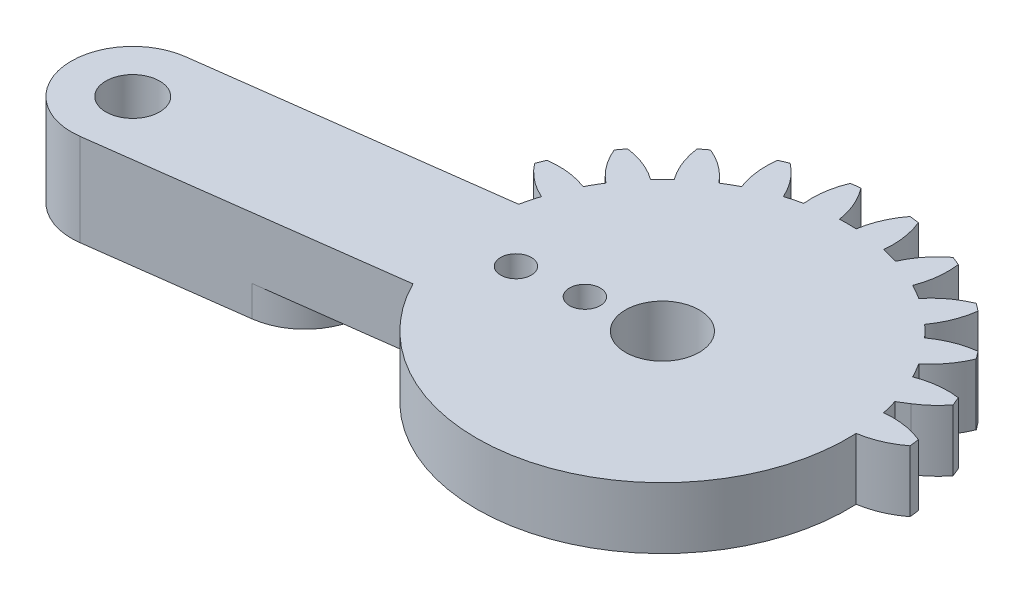
SolidWorks part; units mm, degrees
ref_plane "Front Plane" through (0, 0, 0) normal (0, 0, 1) x (1, 0, 0)
ref_plane "Top Plane" through (0, 0, 0) normal (0, 1, 0) x (1, 0, 0)
ref_plane "Right Plane" through (0, 0, 0) normal (1, 0, 0) x (0, 0, -1)
sketch "Sketch1" plane through (0, 0, 0) normal (0, 1, 0) x (1, 0, 0)
  line L0 (20.6437, 4) -> (2.0816, 4)
  line L1 (2.0816, -4) -> (20.6437, -4)
  arc A0 (2.0816, 4) -> (3.5217, 5.3071) centre (-0.7683, 8.5867) ccw
  arc A1 (3.5217, 5.3071) -> (3.2829, 5.8838) centre (-10.1063, 0) ccw
  arc A2 (3.2829, 5.8838) -> (0.6271, 5.5703) centre (2.5684, 0.5313) ccw
  arc A3 (0.6271, 5.5703) -> (0.0844, 6.5103) centre (-10.1063, 0) ccw
  arc A4 (0.0844, 6.5103) -> (1.6838, 8.6535) centre (-3.3089, 10.711) ccw
  arc A5 (1.6838, 8.6535) -> (1.3038, 9.1487) centre (-10.1063, 0) ccw
  arc A6 (1.3038, 9.1487) -> (-1.1803, 8.1585) centre (1.999, 3.7936) ccw
  arc A7 (-1.1803, 8.1585) -> (-1.9479, 8.926) centre (-10.1063, 0) ccw
  arc A8 (-1.9479, 8.926) -> (-0.9576, 11.4102) centre (-6.3127, 12.1053) ccw
  arc A9 (-0.9576, 11.4102) -> (-1.4528, 11.7901) centre (-10.1063, 0) ccw
  arc A10 (-1.4528, 11.7901) -> (-3.596, 10.1907) centre (0.6046, 6.7975) ccw
  arc A11 (-3.596, 10.1907) -> (-4.5361, 10.7334) centre (-10.1063, 0) ccw
  arc A12 (-4.5361, 10.7334) -> (-4.2225, 13.3892) centre (-9.5751, 12.6747) ccw
  arc A13 (-4.2225, 13.3892) -> (-4.7992, 13.6281) centre (-10.1063, 0) ccw
  arc A14 (-4.7992, 13.6281) -> (-6.4554, 11.5285) centre (-1.5196, 9.3381) ccw
  arc A15 (-6.4554, 11.5285) -> (-7.5039, 11.8094) centre (-10.1063, 0) ccw
  arc A16 (-7.5039, 11.8094) -> (-7.8884, 14.4558) centre (-12.8736, 12.3803) ccw
  arc A17 (-7.8884, 14.4558) -> (-8.5072, 14.5373) centre (-10.1063, 0) ccw
  arc A18 (-8.5072, 14.5373) -> (-9.5636, 12.0806) centre (-4.2291, 11.2423) ccw
  arc A19 (-9.5636, 12.0806) -> (-10.6491, 12.0806) centre (-10.1063, 0) ccw
  arc A20 (-10.6491, 12.0806) -> (-11.7054, 14.5373) centre (-15.9836, 11.2423) ccw
  arc A21 (-11.7054, 14.5373) -> (-12.3243, 14.4558) centre (-10.1063, 0) ccw
  arc A22 (-12.3243, 14.4558) -> (-12.7088, 11.8094) centre (-7.3391, 12.3803) ccw
  arc A23 (-12.7088, 11.8094) -> (-13.7573, 11.5285) centre (-10.1063, 0) ccw
  arc A24 (-13.7573, 11.5285) -> (-15.4135, 13.6281) centre (-18.6931, 9.3381) ccw
  arc A25 (-15.4135, 13.6281) -> (-15.9901, 13.3892) centre (-10.1063, 0) ccw
  arc A26 (-15.9901, 13.3892) -> (-15.6766, 10.7334) centre (-10.6376, 12.6747) ccw
  arc A27 (-15.6766, 10.7334) -> (-16.6166, 10.1907) centre (-10.1063, 0) ccw
  arc A28 (-16.6166, 10.1907) -> (-18.7599, 11.7901) centre (-20.8173, 6.7975) ccw
  arc A29 (-18.7599, 11.7901) -> (-19.255, 11.4102) centre (-10.1063, 0) ccw
  arc A30 (-19.255, 11.4102) -> (-18.2648, 8.926) centre (-13.9, 12.1053) ccw
  arc A31 (-18.2648, 8.926) -> (-19.0324, 8.1585) centre (-10.1063, 0) ccw
  arc A32 (-19.0324, 8.1585) -> (-21.5165, 9.1487) centre (-22.2117, 3.7936) ccw
  arc A33 (-21.5165, 9.1487) -> (-21.8965, 8.6535) centre (-10.1063, 0) ccw
  arc A34 (-21.8965, 8.6535) -> (-20.2971, 6.5103) centre (-16.9038, 10.711) ccw
  arc A35 (-20.2971, 6.5103) -> (-20.8398, 5.5703) centre (-10.1063, 0) ccw
  arc A36 (-20.8398, 5.5703) -> (-23.4956, 5.8838) centre (-22.7811, 0.5313) ccw
  arc A37 (-23.4956, 5.8838) -> (-23.7344, 5.3071) centre (-10.1063, 0) ccw
  arc A38 (-23.7344, 5.3071) -> (-21.6348, 3.6509) centre (-19.4444, 8.5867) ccw
  arc A39 (-21.6348, 3.6509) -> (-21.9157, 2.6025) centre (-10.1063, 0) ccw
  arc A40 (-21.9157, 2.6025) -> (-24.5622, 2.2179) centre (-22.4867, -2.7673) ccw
  arc A41 (-24.5622, 2.2179) -> (-24.6437, 1.5991) centre (-10.1063, 0) ccw
  arc A42 (-24.6437, 1.5991) -> (-22.1869, 0.5427) centre (-21.3486, 5.8773) ccw
  arc A43 (-22.1869, 0.5427) -> (-22.1869, -0.5427) centre (-10.1063, 0) ccw
  arc A44 (-22.1869, -0.5427) -> (-24.6437, -1.5991) centre (-21.3486, -5.8773) ccw
  arc A45 (-24.6437, -1.5991) -> (-24.5622, -2.2179) centre (-10.1063, 0) ccw
  arc A46 (-24.5622, -2.2179) -> (-21.9157, -2.6025) centre (-22.4867, 2.7673) ccw
  arc A47 (-21.9157, -2.6025) -> (-21.6348, -3.6509) centre (-10.1063, 0) ccw
  arc A48 (-21.6348, -3.6509) -> (-23.7344, -5.3071) centre (-19.4444, -8.5867) ccw
  arc A49 (-23.7344, -5.3071) -> (-23.4956, -5.8838) centre (-10.1063, 0) ccw
  arc A50 (-23.4956, -5.8838) -> (-20.8398, -5.5703) centre (-22.7811, -0.5313) ccw
  arc A51 (-20.8398, -5.5703) -> (-20.2971, -6.5103) centre (-10.1063, 0) ccw
  arc A52 (-20.2971, -6.5103) -> (-21.8965, -8.6535) centre (-16.9038, -10.711) ccw
  arc A53 (-21.8965, -8.6535) -> (-21.5165, -9.1487) centre (-10.1063, 0) ccw
  arc A54 (-21.5165, -9.1487) -> (-19.0324, -8.1585) centre (-22.2117, -3.7936) ccw
  arc A55 (-19.0324, -8.1585) -> (-18.2648, -8.926) centre (-10.1063, 0) ccw
  arc A56 (-18.2648, -8.926) -> (-19.255, -11.4102) centre (-13.9, -12.1053) ccw
  arc A57 (-19.255, -11.4102) -> (-18.7599, -11.7901) centre (-10.1063, 0) ccw
  arc A58 (-18.7599, -11.7901) -> (-16.6166, -10.1907) centre (-20.8173, -6.7975) ccw
  arc A59 (-16.6166, -10.1907) -> (-15.6766, -10.7334) centre (-10.1063, 0) ccw
  arc A60 (-15.6766, -10.7334) -> (-15.9901, -13.3892) centre (-10.6376, -12.6747) ccw
  arc A61 (-15.9901, -13.3892) -> (-15.4135, -13.6281) centre (-10.1063, 0) ccw
  arc A62 (-15.4135, -13.6281) -> (-13.7573, -11.5285) centre (-18.6931, -9.3381) ccw
  arc A63 (-13.7573, -11.5285) -> (-12.7088, -11.8094) centre (-10.1063, 0) ccw
  arc A64 (-12.7088, -11.8094) -> (-12.3243, -14.4558) centre (-7.3391, -12.3803) ccw
  arc A65 (-12.3243, -14.4558) -> (-11.7054, -14.5373) centre (-10.1063, 0) ccw
  arc A66 (-11.7054, -14.5373) -> (-10.6491, -12.0806) centre (-15.9836, -11.2423) ccw
  arc A67 (-10.6491, -12.0806) -> (-9.5636, -12.0806) centre (-10.1063, 0) ccw
  arc A68 (-9.5636, -12.0806) -> (-8.5072, -14.5373) centre (-4.2291, -11.2423) ccw
  arc A69 (-8.5072, -14.5373) -> (-7.8884, -14.4558) centre (-10.1063, 0) ccw
  arc A70 (-7.8884, -14.4558) -> (-7.5039, -11.8094) centre (-12.8736, -12.3803) ccw
  arc A71 (-7.5039, -11.8094) -> (-6.4554, -11.5285) centre (-10.1063, 0) ccw
  arc A72 (-6.4554, -11.5285) -> (-4.7992, -13.6281) centre (-1.5196, -9.3381) ccw
  arc A73 (-4.7992, -13.6281) -> (-4.2225, -13.3892) centre (-10.1063, 0) ccw
  arc A74 (-4.2225, -13.3892) -> (-4.5361, -10.7334) centre (-9.5751, -12.6747) ccw
  arc A75 (-4.5361, -10.7334) -> (-3.596, -10.1907) centre (-10.1063, 0) ccw
  arc A76 (-3.596, -10.1907) -> (-1.4528, -11.7901) centre (0.6046, -6.7975) ccw
  arc A77 (-1.4528, -11.7901) -> (-0.9576, -11.4102) centre (-10.1063, 0) ccw
  arc A78 (-0.9576, -11.4102) -> (-1.9479, -8.926) centre (-6.3127, -12.1053) ccw
  arc A79 (-1.9479, -8.926) -> (-1.1803, -8.1585) centre (-10.1063, 0) ccw
  arc A80 (-1.1803, -8.1585) -> (1.3038, -9.1487) centre (1.999, -3.7936) ccw
  arc A81 (1.3038, -9.1487) -> (1.6838, -8.6535) centre (-10.1063, 0) ccw
  arc A82 (1.6838, -8.6535) -> (0.0844, -6.5103) centre (-3.3089, -10.711) ccw
  arc A83 (0.0844, -6.5103) -> (0.6271, -5.5703) centre (-10.1063, 0) ccw
  arc A84 (0.6271, -5.5703) -> (3.2829, -5.8838) centre (2.5684, -0.5313) ccw
  arc A85 (3.2829, -5.8838) -> (3.5217, -5.3071) centre (-10.1063, 0) ccw
  arc A86 (3.5217, -5.3071) -> (2.0816, -4) centre (-0.7683, -8.5867) ccw
  arc A87 (20.6437, -4) -> (20.6437, 4) centre (20.6437, 0) ccw
  circle A88 centre (-10.1063, 0) radius 1.5
  circle A89 centre (20.6437, 0) radius 1.5
  dimension "D1" = 3
  dimension "D2" = 3
extrude "Boss-Extrude1" add sketch "Sketch1" along normal blind 4
sketch "Sketch3" plane through (0, 4, 0) normal (0, 1, 0) x (1, 0, 0)
  line L0 (-10.1063, 0) -> (-40.8563, 0) construction
  line L1 (-10.1063, 0) -> (-40.5933, -4.0137)
  line L2 (-10.6284, 3.9658) -> (-41.1154, -0.0479)
  line L3 (-9.5842, -3.9658) -> (-40.0712, -7.9795)
  line L4 (-10.1063, 0) -> (-4.5096, 13.5117) construction
  line L5 (-10.1063, 0) -> (-8.1974, 14.4999) construction
  circle A0 centre (-10.1063, 0) radius 1.5
  circle A1 centre (20.6437, 0) radius 1.5 construction
  circle A2 centre (20.6437, 0) radius 1.5
  circle A3 centre (-40.5933, -4.0137) radius 1.75
  circle A4 centre (-40.5933, -4.0137) radius 4
  circle A5 centre (-10.1063, 0) radius 4
  arc A6 (-4.2225, 13.3892) -> (-4.7992, 13.6281) centre (-10.1063, 0) ccw construction
  arc A7 (-7.8884, 14.4558) -> (-8.5072, 14.5373) centre (-10.1063, 0) ccw construction
  dimension "D2" = 3
  dimension "D5" = 3.5
  dimension "D6" = 8
  dimension "D7" = 8
  dimension "D1" = 30.75
  dimension "D4" = 7.5
extrude "Boss-Extrude2" add sketch "Sketch3" against normal blind 4
sketch "Sketch4" plane through (0, 4, 0) normal (0, 1, 0) x (1, 0, 0)
  line L0 (20.6437, 4) -> (2.0816, 4) construction
  line L1 (2.0816, -4) -> (20.6437, -4) construction
  line L2 (20.6437, 4) -> (2.0816, 4)
  line L3 (2.0816, -4) -> (20.6437, -4)
  line L4 (2.0816, 4) -> (1.4381, 3.6001)
  line L5 (-21.6245, -5.5509) -> (-20.8986, -5.4553)
  line L6 (-10.1063, 0) -> (0.0844, 6.5103) construction
  line L7 (-10.1063, 0) -> (1.9742, 0.5427) construction
  line L8 (-24.5755, 2.1296) -> (-41.1154, -0.0479)
  line L9 (-40.0712, -7.9795) -> (-23.5312, -5.8019)
  line L10 (2.0816, -4) -> (20.6437, -4)
  line L11 (20.6437, 4) -> (2.0816, 4)
  line L12 (-21.9429, 2.4762) -> (-41.1154, -0.0479)
  line L13 (-40.0712, -7.9795) -> (-21.6245, -5.5509)
  line L14 (2.0816, -4) -> (20.6437, -4)
  line L15 (20.6437, 4) -> (2.0816, 4)
  circle A0 centre (-10.1063, 0) radius 12.0927
  arc A1 (3.2829, 5.8838) -> (0.6271, 5.5703) centre (2.5684, 0.5313) ccw construction
  arc A2 (3.5217, 5.3071) -> (3.2829, 5.8838) centre (-10.1063, 0) ccw construction
  arc A3 (2.0816, 4) -> (3.5217, 5.3071) centre (-0.7683, 8.5867) ccw construction
  arc A4 (20.6437, -4) -> (20.6437, 4) centre (20.6437, 0) ccw construction
  arc A5 (3.5217, -5.3071) -> (2.0816, -4) centre (-0.7683, -8.5867) ccw construction
  arc A6 (3.2829, -5.8838) -> (3.5217, -5.3071) centre (-10.1063, 0) ccw construction
  arc A7 (0.6271, -5.5703) -> (3.2829, -5.8838) centre (2.5684, -0.5313) ccw construction
  arc A8 (3.2829, 5.8838) -> (0.6271, 5.5703) centre (2.5684, 0.5313) ccw
  arc A9 (3.5217, 5.3071) -> (3.2829, 5.8838) centre (-10.1063, 0) ccw
  arc A10 (2.0816, 4) -> (3.5217, 5.3071) centre (-0.7683, 8.5867) ccw
  arc A11 (20.6437, -4) -> (20.6437, 4) centre (20.6437, 0) ccw
  arc A12 (3.5217, -5.3071) -> (2.0816, -4) centre (-0.7683, -8.5867) ccw
  arc A13 (3.2829, -5.8838) -> (3.5217, -5.3071) centre (-10.1063, 0) ccw
  arc A14 (0.6271, -5.5703) -> (3.2829, -5.8838) centre (2.5684, -0.5313) ccw
  arc A15 (1.9742, 0.5427) -> (4.431, 1.5991) centre (1.1359, 5.8773) ccw
  arc A16 (4.3495, 2.2179) -> (1.7031, 2.6025) centre (2.274, -2.7673) ccw
  arc A17 (4.431, 1.5991) -> (4.3495, 2.2179) centre (-10.1063, 0) ccw
  arc A95 (-21.6348, 3.6509) -> (-21.9157, 2.6025) centre (-10.1063, 0) ccw
  arc A96 (-41.1154, -0.0479) -> (-40.0712, -7.9795) centre (-40.5933, -4.0137) ccw
  arc A97 (-20.2971, -6.5103) -> (-21.8965, -8.6535) centre (-16.9038, -10.711) ccw
  arc A98 (-21.8965, -8.6535) -> (-21.5165, -9.1487) centre (-10.1063, 0) ccw
  arc A99 (-21.5165, -9.1487) -> (-19.0324, -8.1585) centre (-22.2117, -3.7936) ccw
  arc A100 (-19.0324, -8.1585) -> (-18.2648, -8.926) centre (-10.1063, 0) ccw
  arc A101 (-18.2648, -8.926) -> (-19.255, -11.4102) centre (-13.9, -12.1053) ccw
  arc A102 (-19.255, -11.4102) -> (-18.7599, -11.7901) centre (-10.1063, 0) ccw
  arc A103 (-18.7599, -11.7901) -> (-16.6166, -10.1907) centre (-20.8173, -6.7975) ccw
  arc A104 (-16.6166, -10.1907) -> (-15.6766, -10.7334) centre (-10.1063, 0) ccw
  arc A105 (-15.6766, -10.7334) -> (-15.9901, -13.3892) centre (-10.6376, -12.6747) ccw
  arc A106 (-15.9901, -13.3892) -> (-15.4135, -13.6281) centre (-10.1063, 0) ccw
  arc A107 (-15.4135, -13.6281) -> (-13.7573, -11.5285) centre (-18.6931, -9.3381) ccw
  arc A108 (-13.7573, -11.5285) -> (-12.7088, -11.8094) centre (-10.1063, 0) ccw
  arc A109 (-12.7088, -11.8094) -> (-12.3243, -14.4558) centre (-7.3391, -12.3803) ccw
  arc A110 (-12.3243, -14.4558) -> (-11.7054, -14.5373) centre (-10.1063, 0) ccw
  arc A111 (-11.7054, -14.5373) -> (-10.6491, -12.0806) centre (-15.9836, -11.2423) ccw
  arc A112 (-10.6491, -12.0806) -> (-9.5636, -12.0806) centre (-10.1063, 0) ccw
  arc A113 (-9.5636, -12.0806) -> (-8.5072, -14.5373) centre (-4.2291, -11.2423) ccw
  arc A114 (-8.5072, -14.5373) -> (-7.8884, -14.4558) centre (-10.1063, 0) ccw
  arc A115 (-7.8884, -14.4558) -> (-7.5039, -11.8094) centre (-12.8736, -12.3803) ccw
  arc A116 (-7.5039, -11.8094) -> (-6.4554, -11.5285) centre (-10.1063, 0) ccw
  arc A117 (-6.4554, -11.5285) -> (-4.7992, -13.6281) centre (-1.5196, -9.3381) ccw
  arc A118 (-4.7992, -13.6281) -> (-4.2225, -13.3892) centre (-10.1063, 0) ccw
  arc A119 (-4.2225, -13.3892) -> (-4.5361, -10.7334) centre (-9.5751, -12.6747) ccw
  arc A120 (-4.5361, -10.7334) -> (-3.596, -10.1907) centre (-10.1063, 0) ccw
  arc A121 (-3.596, -10.1907) -> (-1.4528, -11.7901) centre (0.6046, -6.7975) ccw
  arc A122 (-1.4528, -11.7901) -> (-0.9576, -11.4102) centre (-10.1063, 0) ccw
  arc A123 (-0.9576, -11.4102) -> (-1.9479, -8.926) centre (-6.3127, -12.1053) ccw
  arc A124 (-1.9479, -8.926) -> (-1.1803, -8.1585) centre (-10.1063, 0) ccw
  arc A125 (-1.1803, -8.1585) -> (1.3038, -9.1487) centre (1.999, -3.7936) ccw
  arc A126 (1.3038, -9.1487) -> (1.6838, -8.6535) centre (-10.1063, 0) ccw
  arc A127 (1.6838, -8.6535) -> (0.0844, -6.5103) centre (-3.3089, -10.711) ccw
  arc A128 (0.0844, -6.5103) -> (0.6271, -5.5703) centre (-10.1063, 0) ccw
  arc A129 (0.6271, -5.5703) -> (3.2829, -5.8838) centre (2.5684, -0.5313) ccw
  arc A130 (3.2829, -5.8838) -> (3.5217, -5.3071) centre (-10.1063, 0) ccw
  arc A131 (3.5217, -5.3071) -> (2.0816, -4) centre (-0.7683, -8.5867) ccw
  arc A132 (20.6437, -4) -> (20.6437, 4) centre (20.6437, 0) ccw
  arc A133 (2.0816, 4) -> (3.5217, 5.3071) centre (-0.7683, 8.5867) ccw
  arc A134 (3.5217, 5.3071) -> (3.2829, 5.8838) centre (-10.1063, 0) ccw
  arc A135 (3.2829, 5.8838) -> (0.6271, 5.5703) centre (2.5684, 0.5313) ccw
  arc A136 (0.6271, 5.5703) -> (0.0844, 6.5103) centre (-10.1063, 0) ccw
  arc A137 (0.0844, 6.5103) -> (1.6838, 8.6535) centre (-3.3089, 10.711) ccw
  arc A138 (1.6838, 8.6535) -> (1.3038, 9.1487) centre (-10.1063, 0) ccw
  arc A139 (1.3038, 9.1487) -> (-1.1803, 8.1585) centre (1.999, 3.7936) ccw
  arc A140 (-1.1803, 8.1585) -> (-1.9479, 8.926) centre (-10.1063, 0) ccw
  arc A141 (-1.9479, 8.926) -> (-0.9576, 11.4102) centre (-6.3127, 12.1053) ccw
  arc A142 (-0.9576, 11.4102) -> (-1.4528, 11.7901) centre (-10.1063, 0) ccw
  arc A143 (-1.4528, 11.7901) -> (-3.596, 10.1907) centre (0.6046, 6.7975) ccw
  arc A144 (-3.596, 10.1907) -> (-4.5361, 10.7334) centre (-10.1063, 0) ccw
  arc A145 (-4.5361, 10.7334) -> (-4.2225, 13.3892) centre (-9.5751, 12.6747) ccw
  arc A146 (-4.2225, 13.3892) -> (-4.7992, 13.6281) centre (-10.1063, 0) ccw
  arc A147 (-4.7992, 13.6281) -> (-6.4554, 11.5285) centre (-1.5196, 9.3381) ccw
  arc A148 (-6.4554, 11.5285) -> (-7.5039, 11.8094) centre (-10.1063, 0) ccw
  arc A149 (-7.5039, 11.8094) -> (-7.8884, 14.4558) centre (-12.8736, 12.3803) ccw
  arc A150 (-7.8884, 14.4558) -> (-8.5072, 14.5373) centre (-10.1063, 0) ccw
  arc A151 (-8.5072, 14.5373) -> (-9.5636, 12.0806) centre (-4.2291, 11.2423) ccw
  arc A152 (-9.5636, 12.0806) -> (-10.6491, 12.0806) centre (-10.1063, 0) ccw
  arc A153 (-10.6491, 12.0806) -> (-11.7054, 14.5373) centre (-15.9836, 11.2423) ccw
  arc A154 (-11.7054, 14.5373) -> (-12.3243, 14.4558) centre (-10.1063, 0) ccw
  arc A155 (-12.3243, 14.4558) -> (-12.7088, 11.8094) centre (-7.3391, 12.3803) ccw
  arc A156 (-12.7088, 11.8094) -> (-13.7573, 11.5285) centre (-10.1063, 0) ccw
  arc A157 (-13.7573, 11.5285) -> (-15.4135, 13.6281) centre (-18.6931, 9.3381) ccw
  arc A158 (-15.4135, 13.6281) -> (-15.9901, 13.3892) centre (-10.1063, 0) ccw
  arc A159 (-15.9901, 13.3892) -> (-15.6766, 10.7334) centre (-10.6376, 12.6747) ccw
  arc A160 (-15.6766, 10.7334) -> (-16.6166, 10.1907) centre (-10.1063, 0) ccw
  arc A161 (-16.6166, 10.1907) -> (-18.7599, 11.7901) centre (-20.8173, 6.7975) ccw
  arc A162 (-18.7599, 11.7901) -> (-19.255, 11.4102) centre (-10.1063, 0) ccw
  arc A163 (-19.255, 11.4102) -> (-18.2648, 8.926) centre (-13.9, 12.1053) ccw
  arc A164 (-18.2648, 8.926) -> (-19.0324, 8.1585) centre (-10.1063, 0) ccw
  arc A165 (-19.0324, 8.1585) -> (-21.5165, 9.1487) centre (-22.2117, 3.7936) ccw
  arc A166 (-21.5165, 9.1487) -> (-21.8965, 8.6535) centre (-10.1063, 0) ccw
  arc A167 (-21.8965, 8.6535) -> (-20.2971, 6.5103) centre (-16.9038, 10.711) ccw
  arc A168 (-20.2971, 6.5103) -> (-20.8398, 5.5703) centre (-10.1063, 0) ccw
  arc A169 (-20.8398, 5.5703) -> (-23.4956, 5.8838) centre (-22.7811, 0.5313) ccw
  arc A170 (-23.4956, 5.8838) -> (-23.7344, 5.3071) centre (-10.1063, 0) ccw
  arc A171 (-23.7344, 5.3071) -> (-21.6348, 3.6509) centre (-19.4444, 8.5867) ccw
  arc A172 (-21.6348, 3.6509) -> (-21.9157, 2.6025) centre (-10.1063, 0) ccw
  arc A175 (-23.4956, -5.8838) -> (-20.8398, -5.5703) centre (-22.7811, -0.5313) ccw
  arc A176 (-41.1154, -0.0479) -> (-40.0712, -7.9795) centre (-40.5933, -4.0137) ccw
  arc A177 (-20.2971, -6.5103) -> (-21.8965, -8.6535) centre (-16.9038, -10.711) ccw
  arc A178 (-21.8965, -8.6535) -> (-21.5165, -9.1487) centre (-10.1063, 0) ccw
  arc A179 (-21.5165, -9.1487) -> (-19.0324, -8.1585) centre (-22.2117, -3.7936) ccw
  arc A180 (-19.0324, -8.1585) -> (-18.2648, -8.926) centre (-10.1063, 0) ccw
  arc A181 (-18.2648, -8.926) -> (-19.255, -11.4102) centre (-13.9, -12.1053) ccw
  arc A182 (-19.255, -11.4102) -> (-18.7599, -11.7901) centre (-10.1063, 0) ccw
  arc A183 (-18.7599, -11.7901) -> (-16.6166, -10.1907) centre (-20.8173, -6.7975) ccw
  arc A184 (-16.6166, -10.1907) -> (-15.6766, -10.7334) centre (-10.1063, 0) ccw
  arc A185 (-15.6766, -10.7334) -> (-15.9901, -13.3892) centre (-10.6376, -12.6747) ccw
  arc A186 (-15.9901, -13.3892) -> (-15.4135, -13.6281) centre (-10.1063, 0) ccw
  arc A187 (-15.4135, -13.6281) -> (-13.7573, -11.5285) centre (-18.6931, -9.3381) ccw
  arc A188 (-13.7573, -11.5285) -> (-12.7088, -11.8094) centre (-10.1063, 0) ccw
  arc A189 (-12.7088, -11.8094) -> (-12.3243, -14.4558) centre (-7.3391, -12.3803) ccw
  arc A190 (-12.3243, -14.4558) -> (-11.7054, -14.5373) centre (-10.1063, 0) ccw
  arc A191 (-11.7054, -14.5373) -> (-10.6491, -12.0806) centre (-15.9836, -11.2423) ccw
  arc A192 (-10.6491, -12.0806) -> (-9.5636, -12.0806) centre (-10.1063, 0) ccw
  arc A193 (-9.5636, -12.0806) -> (-8.5072, -14.5373) centre (-4.2291, -11.2423) ccw
  arc A194 (-8.5072, -14.5373) -> (-7.8884, -14.4558) centre (-10.1063, 0) ccw
  arc A195 (-7.8884, -14.4558) -> (-7.5039, -11.8094) centre (-12.8736, -12.3803) ccw
  arc A196 (-7.5039, -11.8094) -> (-6.4554, -11.5285) centre (-10.1063, 0) ccw
  arc A197 (-6.4554, -11.5285) -> (-4.7992, -13.6281) centre (-1.5196, -9.3381) ccw
  arc A198 (-4.7992, -13.6281) -> (-4.2225, -13.3892) centre (-10.1063, 0) ccw
  arc A199 (-4.2225, -13.3892) -> (-4.5361, -10.7334) centre (-9.5751, -12.6747) ccw
  arc A200 (-4.5361, -10.7334) -> (-3.596, -10.1907) centre (-10.1063, 0) ccw
  arc A201 (-3.596, -10.1907) -> (-1.4528, -11.7901) centre (0.6046, -6.7975) ccw
  arc A202 (-1.4528, -11.7901) -> (-0.9576, -11.4102) centre (-10.1063, 0) ccw
  arc A203 (-0.9576, -11.4102) -> (-1.9479, -8.926) centre (-6.3127, -12.1053) ccw
  arc A204 (-1.9479, -8.926) -> (-1.1803, -8.1585) centre (-10.1063, 0) ccw
  arc A205 (-1.1803, -8.1585) -> (1.3038, -9.1487) centre (1.999, -3.7936) ccw
  arc A206 (1.3038, -9.1487) -> (1.6838, -8.6535) centre (-10.1063, 0) ccw
  arc A207 (1.6838, -8.6535) -> (0.0844, -6.5103) centre (-3.3089, -10.711) ccw
  arc A208 (0.0844, -6.5103) -> (0.6271, -5.5703) centre (-10.1063, 0) ccw
  arc A209 (0.6271, -5.5703) -> (3.2829, -5.8838) centre (2.5684, -0.5313) ccw
  arc A210 (3.2829, -5.8838) -> (3.5217, -5.3071) centre (-10.1063, 0) ccw
  arc A211 (3.5217, -5.3071) -> (2.0816, -4) centre (-0.7683, -8.5867) ccw
  arc A212 (20.6437, -4) -> (20.6437, 4) centre (20.6437, 0) ccw
  arc A213 (2.0816, 4) -> (3.5217, 5.3071) centre (-0.7683, 8.5867) ccw
  arc A214 (3.5217, 5.3071) -> (3.2829, 5.8838) centre (-10.1063, 0) ccw
  arc A215 (3.2829, 5.8838) -> (0.6271, 5.5703) centre (2.5684, 0.5313) ccw
  arc A216 (0.6271, 5.5703) -> (0.0844, 6.5103) centre (-10.1063, 0) ccw
  arc A217 (0.0844, 6.5103) -> (1.6838, 8.6535) centre (-3.3089, 10.711) ccw
  arc A218 (1.6838, 8.6535) -> (1.3038, 9.1487) centre (-10.1063, 0) ccw
  arc A219 (1.3038, 9.1487) -> (-1.1803, 8.1585) centre (1.999, 3.7936) ccw
  arc A220 (-1.1803, 8.1585) -> (-1.9479, 8.926) centre (-10.1063, 0) ccw
  arc A221 (-1.9479, 8.926) -> (-0.9576, 11.4102) centre (-6.3127, 12.1053) ccw
  arc A222 (-0.9576, 11.4102) -> (-1.4528, 11.7901) centre (-10.1063, 0) ccw
  arc A223 (-1.4528, 11.7901) -> (-3.596, 10.1907) centre (0.6046, 6.7975) ccw
  arc A224 (-3.596, 10.1907) -> (-4.5361, 10.7334) centre (-10.1063, 0) ccw
  arc A225 (-4.5361, 10.7334) -> (-4.2225, 13.3892) centre (-9.5751, 12.6747) ccw
  arc A226 (-4.2225, 13.3892) -> (-4.7992, 13.6281) centre (-10.1063, 0) ccw
  arc A227 (-4.7992, 13.6281) -> (-6.4554, 11.5285) centre (-1.5196, 9.3381) ccw
  arc A228 (-6.4554, 11.5285) -> (-7.5039, 11.8094) centre (-10.1063, 0) ccw
  arc A229 (-7.5039, 11.8094) -> (-7.8884, 14.4558) centre (-12.8736, 12.3803) ccw
  arc A230 (-7.8884, 14.4558) -> (-8.5072, 14.5373) centre (-10.1063, 0) ccw
  arc A231 (-8.5072, 14.5373) -> (-9.5636, 12.0806) centre (-4.2291, 11.2423) ccw
  arc A232 (-9.5636, 12.0806) -> (-10.6491, 12.0806) centre (-10.1063, 0) ccw
  arc A233 (-10.6491, 12.0806) -> (-11.7054, 14.5373) centre (-15.9836, 11.2423) ccw
  arc A234 (-11.7054, 14.5373) -> (-12.3243, 14.4558) centre (-10.1063, 0) ccw
  arc A235 (-12.3243, 14.4558) -> (-12.7088, 11.8094) centre (-7.3391, 12.3803) ccw
  arc A236 (-12.7088, 11.8094) -> (-13.7573, 11.5285) centre (-10.1063, 0) ccw
  arc A237 (-13.7573, 11.5285) -> (-15.4135, 13.6281) centre (-18.6931, 9.3381) ccw
  arc A238 (-15.4135, 13.6281) -> (-15.9901, 13.3892) centre (-10.1063, 0) ccw
  arc A239 (-15.9901, 13.3892) -> (-15.6766, 10.7334) centre (-10.6376, 12.6747) ccw
  arc A240 (-15.6766, 10.7334) -> (-16.6166, 10.1907) centre (-10.1063, 0) ccw
  arc A241 (-16.6166, 10.1907) -> (-18.7599, 11.7901) centre (-20.8173, 6.7975) ccw
  arc A242 (-18.7599, 11.7901) -> (-19.255, 11.4102) centre (-10.1063, 0) ccw
  arc A243 (-19.255, 11.4102) -> (-18.2648, 8.926) centre (-13.9, 12.1053) ccw
  arc A244 (-18.2648, 8.926) -> (-19.0324, 8.1585) centre (-10.1063, 0) ccw
  arc A245 (-19.0324, 8.1585) -> (-21.5165, 9.1487) centre (-22.2117, 3.7936) ccw
  arc A246 (-21.5165, 9.1487) -> (-21.8965, 8.6535) centre (-10.1063, 0) ccw
  arc A247 (-21.8965, 8.6535) -> (-20.2971, 6.5103) centre (-16.9038, 10.711) ccw
  arc A248 (-20.2971, 6.5103) -> (-20.8398, 5.5703) centre (-10.1063, 0) ccw
  arc A249 (-20.8398, 5.5703) -> (-23.4956, 5.8838) centre (-22.7811, 0.5313) ccw
  arc A250 (-23.4956, 5.8838) -> (-23.7344, 5.3071) centre (-10.1063, 0) ccw
  arc A251 (-23.7344, 5.3071) -> (-21.6348, 3.6509) centre (-19.4444, 8.5867) ccw
  arc A252 (-23.4956, -5.8838) -> (-20.8398, -5.5703) centre (-22.7811, -0.5313) ccw
  arc A253 (-20.8398, -5.5703) -> (-20.2971, -6.5103) centre (-10.1063, 0) ccw
  arc A254 (-20.8398, -5.5703) -> (-20.2971, -6.5103) centre (-10.1063, 0) ccw
  arc A255 (-23.5312, -5.8019) -> (-23.4956, -5.8838) centre (-10.1063, 0) ccw
  arc A256 (-23.5312, -5.8019) -> (-23.4956, -5.8838) centre (-10.1063, 0) ccw
  arc A257 (-21.9157, 2.6025) -> (-24.5622, 2.2179) centre (-22.4867, -2.7673) ccw
  arc A258 (-21.9157, 2.6025) -> (-24.5622, 2.2179) centre (-22.4867, -2.7673) ccw
  arc A259 (-24.5622, 2.2179) -> (-24.5755, 2.1296) centre (-10.1063, 0) ccw
  arc A260 (-24.5622, 2.2179) -> (-24.5755, 2.1296) centre (-10.1063, 0) ccw
  point P40 (-10.1063, 0)
  dimension "D2" = 24.1855
  dimension "D4" = 30
  dimension "D1" = 0
  dimension "D3" = 2
extrude "Cut-Extrude1" cut sketch "Sketch4" against normal blind 4 contours A178 A179 A0 L5 A177 | A182 A183 A0 A181 | A186 A187 A0 A185 | A190 A191 A0 A189 | A194 A195 A0 A193 | A198 A199 A0 A197 | A202 A203 A0 A201 | A206 A207 A0 A205 | A258 A260 L12 A0 | L13 A256 A252 A0 L5 | A0 A14 A13 A12 L3 A11 L2 L4
sketch "Sketch5" plane through (0, 4, 0) normal (0, 1, 0) x (1, 0, 0)
  line L0 (-10.1063, 0) -> (-40.5933, -4.0137) construction
  circle A0 centre (-10.1063, 0) radius 2.4
  circle A2 centre (-14.5678, -0.5874) radius 1
  circle A4 centre (-18.5336, -1.1095) radius 1
  dimension "D1" = 4.8
  dimension "D2" = 4.5
  dimension "D3" = 2
  dimension "D4" = 2
  dimension "D5" = 4
extrude "Cut-Extrude2" cut sketch "Sketch5" against normal up to next
sketch "Sketch7" plane through (0, 4, 0) normal (0, 1, 0) x (1, 0, 0)
  circle A0 centre (-10.1063, 0) radius 13.45 construction
  circle A1 centre (-10.1063, 0) radius 13.45
sketch "Sketch8" plane through (0, 0, 0) normal (0, -1, 0) x (1, 0, 0)
  line L0 (-30.6788, 2.7084) -> (-40.5933, 4.0137) construction
  line L1 (-20.8986, 5.4553) -> (-40.0712, 7.9795) construction
  line L2 (-30.1567, 6.6742) -> (-40.0712, 7.9795)
  line L3 (-21.9429, -2.4762) -> (-41.1154, 0.0479) construction
  line L4 (-31.2009, -1.2574) -> (-41.1154, 0.0479)
  arc A0 (-31.2009, -1.2574) -> (-30.1567, 6.6742) centre (-30.6788, 2.7084) ccw
  arc A1 (-40.0712, 7.9795) -> (-41.1154, 0.0479) centre (-40.5933, 4.0137) ccw construction
  arc A2 (-40.0712, 7.9795) -> (-41.1154, 0.0479) centre (-40.5933, 4.0137) ccw
  circle A3 centre (-40.5933, 4.0137) radius 1.75 construction
  circle A4 centre (-40.5933, 4.0137) radius 1.75
  point P11 (-30.6788, 2.7084)
  point P12 (-30.8445, 2.7084)
  dimension "D1" = 10
extrude "Boss-Extrude3" add sketch "Sketch8" along normal blind 2
